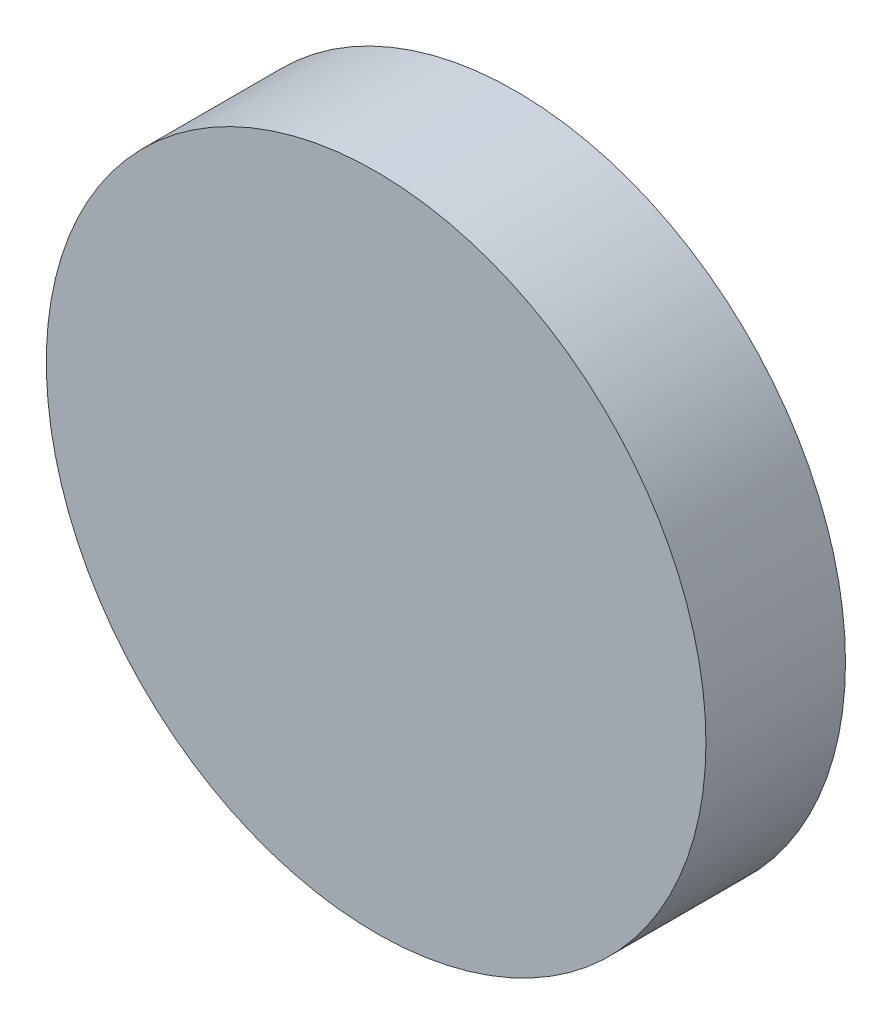
SolidWorks part; units mm, degrees
ref_plane "Front Plane" through (0, 0, 0) normal (0, 0, 1) x (1, 0, 0)
ref_plane "Top Plane" through (0, 0, 0) normal (0, 1, 0) x (1, 0, 0)
ref_plane "Right Plane" through (0, 0, 0) normal (1, 0, 0) x (0, 0, -1)
sketch "Sketch1" plane through (0, 0, 0) normal (0, 0, 1) x (1, 0, 0)
  circle A0 centre (0, 0) radius 26
  dimension "D1" = 52
extrude "Boss-Extrude1" add sketch "Sketch1" along normal blind 11
